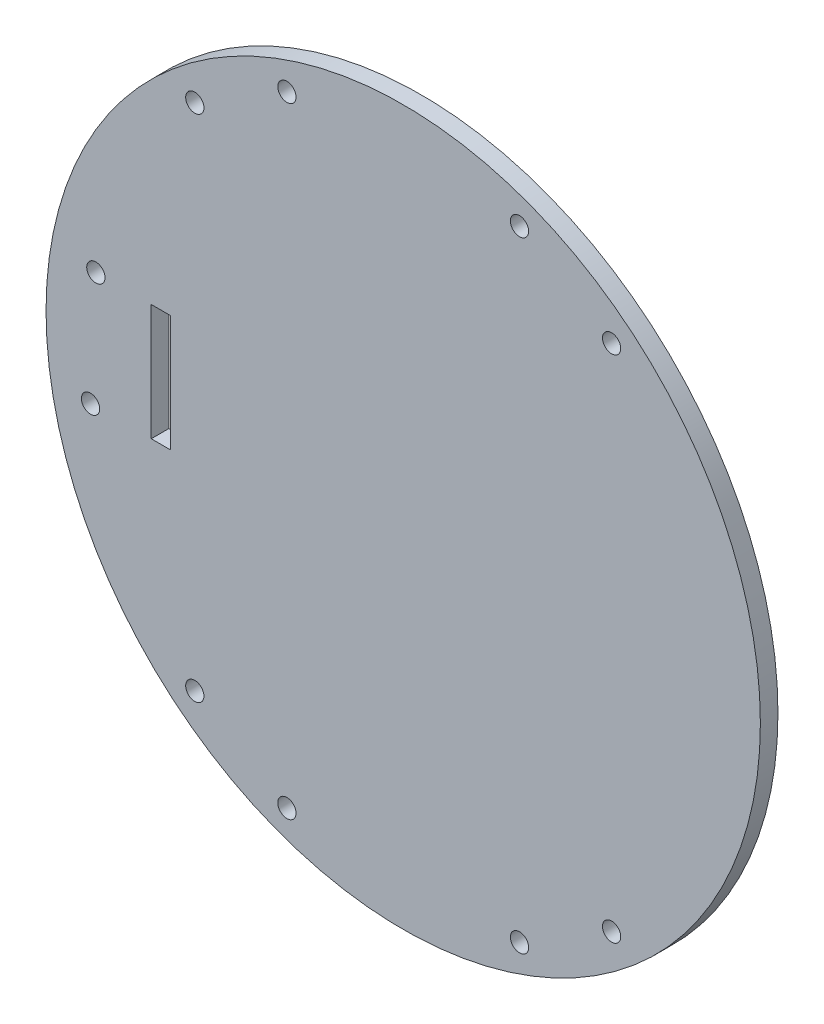
SolidWorks part; units mm, degrees
material "Acrylic (Medium-high impact)"
ref_plane "Front Plane" through (0, 0, 0) normal (0, 0, 1) x (1, 0, 0)
ref_plane "Top Plane" through (0, 0, 0) normal (0, 1, 0) x (1, 0, 0)
ref_plane "Right Plane" through (0, 0, 0) normal (1, 0, 0) x (0, 0, -1)
sketch "Sketch1" plane through (0, 0, 0) normal (0, 0, 1) x (-1, 0, 0)
  line L1 (56.9423, -16.1336) -> (60.4423, -16.1336)
  line L2 (14.9423, 58.8664) -> (14.9423, -70.1336) construction
  line L3 (56.9423, -16.1336) -> (56.9423, 4.8664)
  line L4 (56.9423, 4.8664) -> (60.4423, 4.8664)
  line L5 (79.4423, -5.6336) -> (-49.5577, -5.6336) construction
  line L6 (60.4423, -16.1336) -> (60.4423, 4.8664)
  line L7 (56.9423, -16.1336) -> (60.4423, 4.8664) construction
  line L8 (56.9423, 4.8664) -> (60.4423, -16.1336) construction
  circle A1 centre (14.9423, -5.6336) radius 64.5
  circle A15 centre (-6.0577, 50.3664) radius 1.65
  circle A16 centre (-22.6919, 40.3664) radius 1.65
  circle A17 centre (35.9423, 50.3664) radius 1.65
  circle A18 centre (52.5764, 40.3664) radius 1.65
  circle A19 centre (52.5764, -51.6336) radius 1.65
  circle A20 centre (35.9423, -61.6336) radius 1.65
  circle A21 centre (-6.0577, -61.6336) radius 1.65
  circle A22 centre (-22.6919, -51.6336) radius 1.65
  circle A25 centre (71.404, 4.8664) radius 1.65
  circle A26 centre (70.4423, -16.1336) radius 1.65
  point P0 (58.6923, -5.6336)
  dimension "D3" = 10.5
  dimension "D4" = 10.5
  dimension "D9" = 42
  dimension "D10" = 3.3
  dimension "D11" = 56
  dimension "D20" = 129
  dimension "D5" = 3.3
  dimension "D6" = 3.5
  dimension "D7" = 21
  dimension "D8" = 10
  dimension "D14" = 21
extrude "Boss-Extrude1" add sketch "Sketch1" along normal blind 3.175
